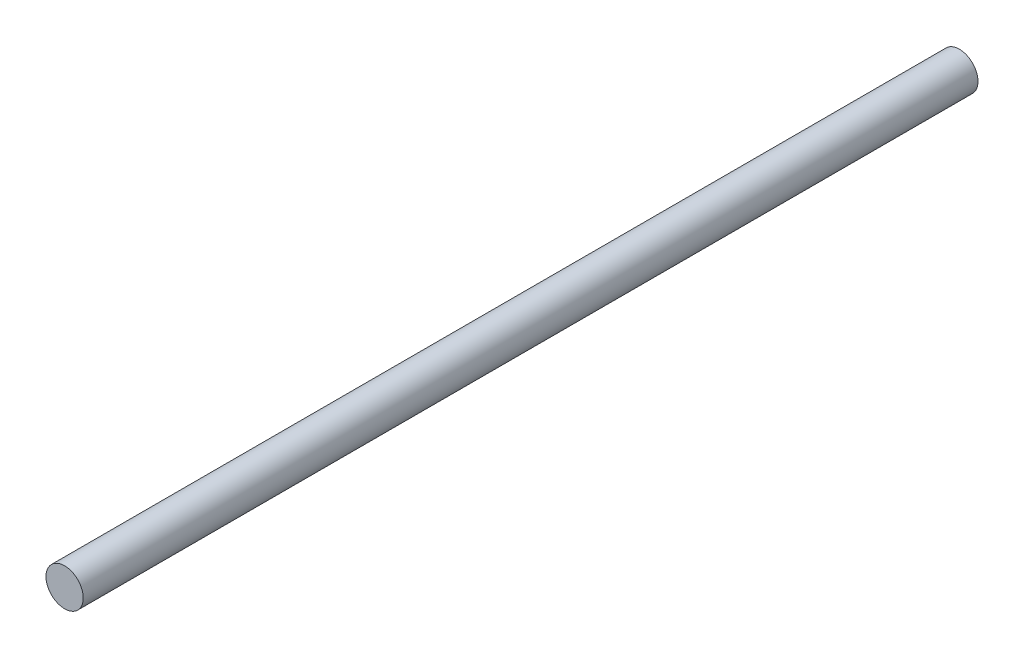
SolidWorks part; units mm, degrees
ref_plane "Front Plane" through (0, 0, 0) normal (0, 0, 1) x (1, 0, 0)
ref_plane "Top Plane" through (0, 0, 0) normal (0, 1, 0) x (1, 0, 0)
ref_plane "Right Plane" through (0, 0, 0) normal (1, 0, 0) x (0, 0, -1)
sketch "Sketch1" plane through (0, 0, 0) normal (0, 0, 1) x (1, 0, 0)
  circle A0 centre (0, 0) radius 15.875
  dimension "D1" = 31.75
extrude "Boss-Extrude1" add sketch "Sketch1" along normal blind 762
